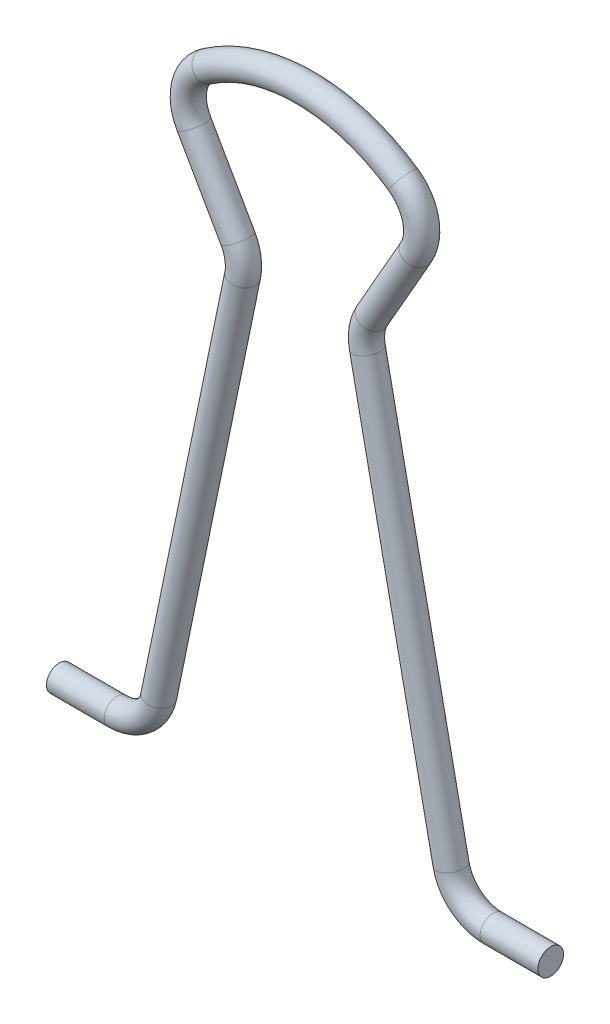
SolidWorks part; units mm, degrees
material "1.4301 (X5CrNi18-10)"
ref_plane "Front Plane" through (0, 0, 0) normal (0, 0, 1) x (1, 0, 0)
ref_plane "Top Plane" through (0, 0, 0) normal (0, 1, 0) x (1, 0, 0)
ref_plane "Right Plane" through (0, 0, 0) normal (1, 0, 0) x (0, 0, -1)
sketch "Sketch1" plane through (0, 0, 0) normal (0, 0, 1) x (1, 0, 0)
  line L0 (-17.25, 0) -> (-13.1944, 0)
  line L1 (-10.2562, 2.394) -> (-4.3788, 30.8909)
  line L2 (-4.7112, 32.9836) -> (-7.7974, 38.3923)
  line L3 (0, 44.5) -> (5.0927, 44.5) construction
  line L4 (0, 44.5) -> (0, 0) construction
  arc A0 (-6.8986, 42.3462) -> (0, 44.5) centre (0, 32.375) cw
  arc A1 (-13.1944, 0) -> (-10.2562, 2.394) centre (-13.1944, 3) ccw
  arc A2 (-4.3788, 30.8909) -> (-4.7112, 32.9836) centre (-7.3169, 31.4969) ccw
  arc A3 (-6.8986, 42.3462) -> (-7.7974, 38.3923) centre (-5.1917, 39.8791) ccw
  point P13 (-10.75, 0)
  point P16 (-4.15, 32)
  point P19 (-9, 40.5)
  dimension "D9" = 3
  dimension "D1" = 32
  dimension "D2" = 44.5
  dimension "D3" = 6.5
  dimension "D4" = 21.5
  dimension "D5" = 4
  dimension "D7" = 18
  dimension "D8" = 8.3
sweep "Sweep1" add path "Sketch1" circular profile diameter 1.8 parameters "D3"=1.8
mirror "Mirror1" about plane through (0, 0, 0) normal (1, 0, 0) of "Sweep1"
ref_plane "PLANE_BASE" through (0, -0.9, 0) normal (0, -1, 0) x (-1, 0, 0)
equation "\"diameter\"=1.8"
equation "\"D3@Sweep1\"=\"diameter\""
